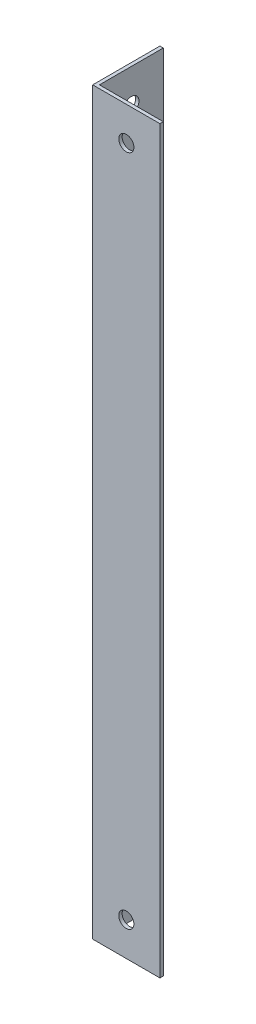
SolidWorks part; units mm, degrees
material "1060 Сплав"
ref_plane "Спереди" through (0, 0, 0) normal (0, 0, 1) x (1, 0, 0)
ref_plane "Сверху" through (0, 0, 0) normal (0, 1, 0) x (1, 0, 0)
ref_plane "Справа" through (0, 0, 0) normal (1, 0, 0) x (0, 0, -1)
sketch "Эскиз1" plane through (0, 0, 0) normal (0, 1, 0) x (1, 0, 0)
  line L0 (0, 0) -> (0, 20)
  line L1 (0, 20) -> (1, 20)
  line L2 (1, 20) -> (1, 1)
  line L3 (1, 1) -> (20, 1)
  line L4 (20, 1) -> (20, 0)
  line L5 (20, 0) -> (0, 0)
  dimension "D1" = 1
  dimension "D2" = 20
extrude "Бобышка-Вытянуть1" add sketch "Эскиз1" along normal blind 220
sketch "Эскиз2" plane through (1, 0, 0) normal (1, 0, 0) x (0, 0, -1)
  line L0 (10.5, 220) -> (10.5, 0) construction
  line L1 (1, 220) -> (20, 220) construction
  line L2 (1, 0) -> (20, 0) construction
  circle A0 centre (10.5, 180) radius 4.25
  circle A1 centre (10.5, 120) radius 4.25
  circle A2 centre (10.5, 60) radius 4.25
  dimension "D1" = 40
  dimension "D2" = 8.5
  dimension "D4" = 60
  dimension "D5" = 60
  dimension "D3" = 3
extrude "Вырез-Вытянуть1" cut sketch "Эскиз2" against normal through all
sketch "Эскиз3" plane through (1, 0, 0) normal (1, 0, 0) x (0, 0, -1)
  circle A0 centre (10.5, 10) radius 2.25 construction
  circle A1 centre (10.5, 10) radius 2.25
extrude "Вырез-Вытянуть2" cut sketch "Эскиз3" against normal through all
sketch "Эскиз4" plane through (1, 0, 0) normal (1, 0, 0) x (0, 0, -1)
  circle A0 centre (10.5, 210) radius 2.25 construction
  circle A1 centre (10.5, 210) radius 2.25
extrude "Вырез-Вытянуть3" cut sketch "Эскиз4" against normal through all
sketch "Эскиз5" plane through (0, 0, -1) normal (0, 0, -1) x (-1, 0, 0)
  line L0 (-20, 220) -> (-20, 0) construction
  line L1 (-20, 0) -> (-1, 0) construction
  line L2 (-20, 220) -> (-1, 220) construction
  circle A0 centre (-10, 10) radius 2.25
  circle A1 centre (-10, 210) radius 2.25
  dimension "D1" = 4.5
  dimension "D4" = 4.5
  dimension "D5" = 10
  dimension "D6" = 10
  dimension "D2" = 10
  dimension "D3" = 10
extrude "Вырез-Вытянуть4" cut sketch "Эскиз5" against normal through all
